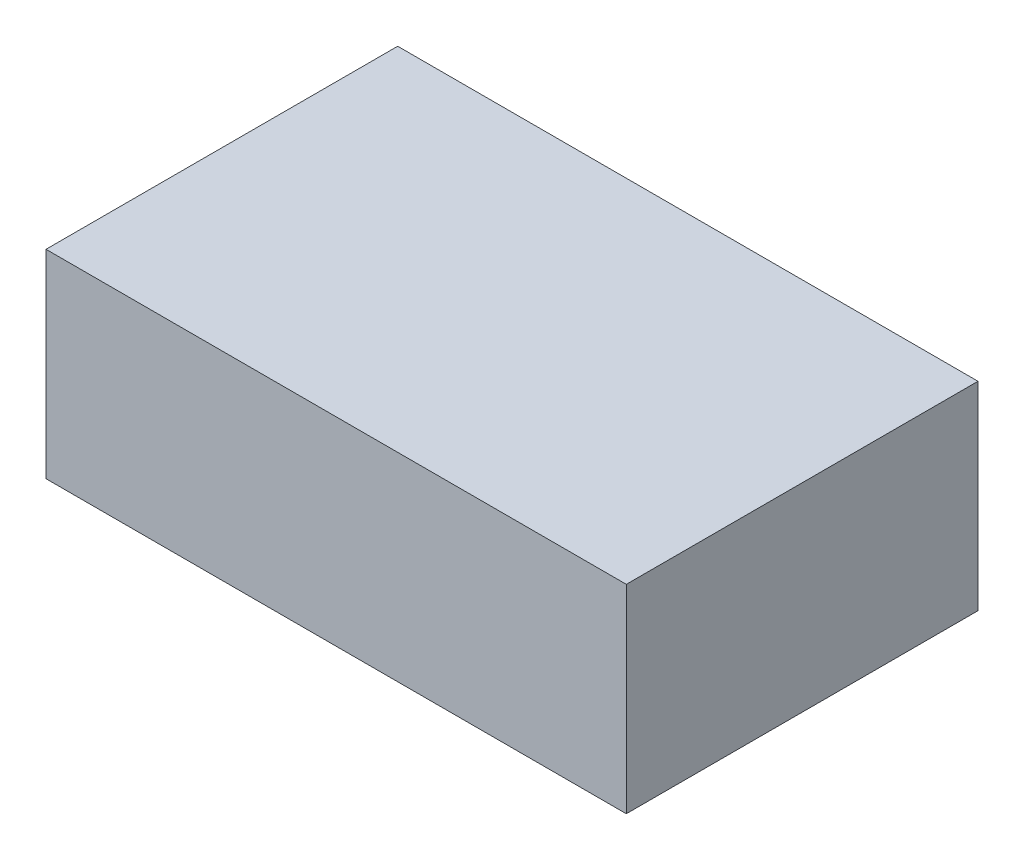
SolidWorks part; units mm, degrees
ref_plane "Front Plane" through (0, 0, 0) normal (0, 0, 1) x (1, 0, 0)
ref_plane "Top Plane" through (0, 0, 0) normal (0, 1, 0) x (1, 0, 0)
ref_plane "Right Plane" through (0, 0, 0) normal (1, 0, 0) x (0, 0, -1)
sketch "Sketch1" plane through (0, 0, 0) normal (0, 1, 0) x (1, 0, 0)
  line L1 (-16.5, 10) -> (16.5, 10)
  line L2 (-16.5, 10) -> (-16.5, -10)
  line L3 (-16.5, -10) -> (16.5, -10)
  line L4 (16.5, 10) -> (16.5, -10)
  point P7 (0, 0)
  dimension "D1" = 10
  dimension "D2" = 10
  dimension "D3" = 16.5
  dimension "D4" = 16.5
extrude "Boss-Extrude1" add sketch "Sketch1" along normal mid plane 11.3
